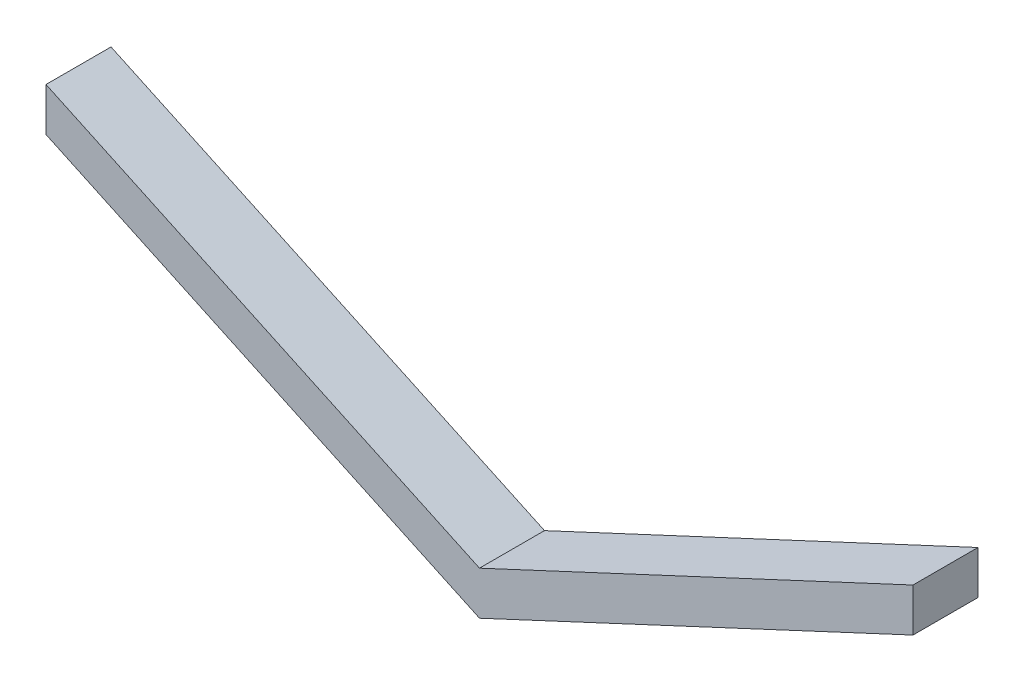
SolidWorks part; units mm, degrees
ref_plane "Plan de face" through (0, 0, 0) normal (0, 0, 1) x (1, 0, 0)
ref_plane "Plan de dessus" through (0, 0, 0) normal (0, 1, 0) x (1, 0, 0)
ref_plane "Plan de droite" through (0, 0, 0) normal (1, 0, 0) x (0, 0, -1)
sketch "Esquisse1" plane through (0, 0, 0) normal (0, 0, 1) x (1, 0, 0)
  line L0 (-200, 113.2615) -> (0, 20)
  line L1 (0, 20) -> (200, 113.2615)
  line L3 (-200, 113.2615) -> (-200, 93.2615)
  line L4 (-200, 93.2615) -> (0, 0)
  line L5 (0, 0) -> (200, 93.2615)
  line L6 (200, 93.2615) -> (200, 113.2615)
  dimension "D1" = 130
  dimension "D2" = 400
  dimension "D3" = 20
  dimension "D4" = 65
  dimension "D5" = 20
  dimension "D6" = 65
extrude "Boss.-Extru.1" add sketch "Esquisse1" along normal blind 30 contours L4 L5 L6 L1 L0 L3
